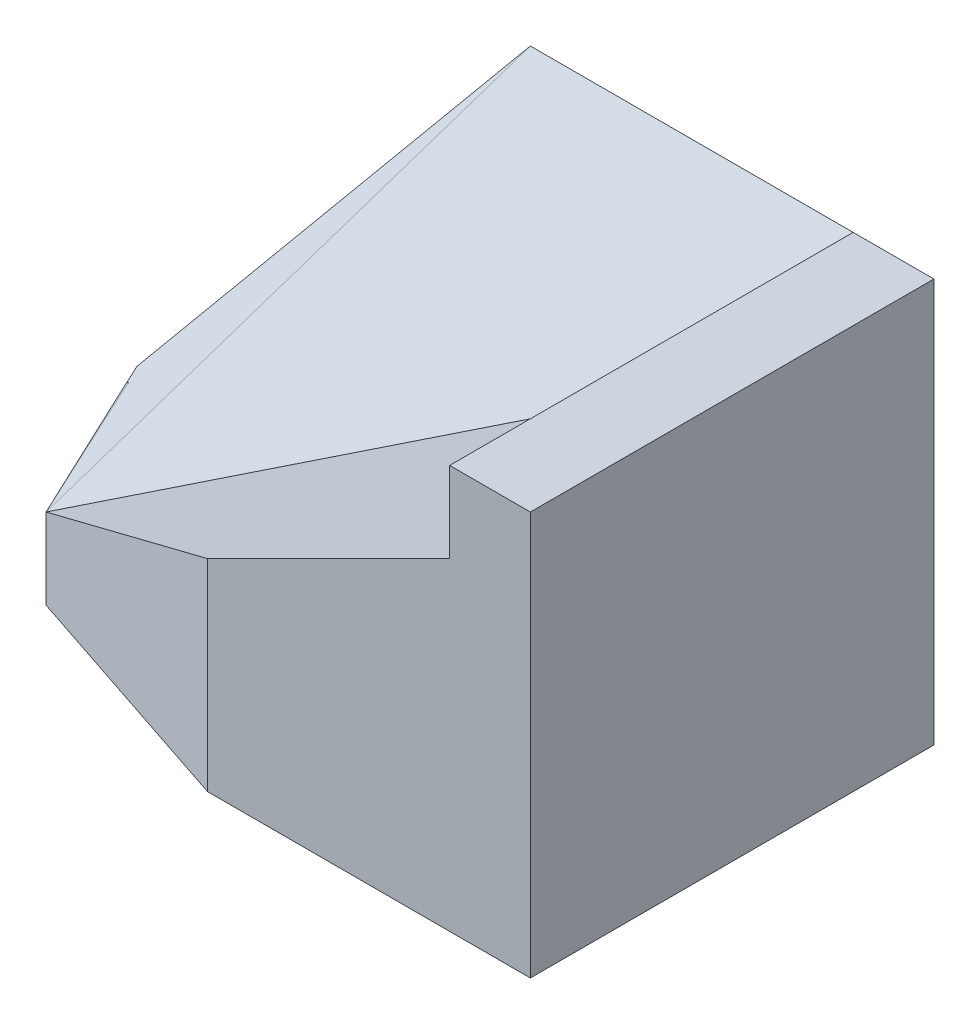
SolidWorks part; units mm, degrees
ref_plane "Front Plane" through (0, 0, 0) normal (0, 0, 1) x (1, 0, 0)
ref_plane "Top Plane" through (0, 0, 0) normal (0, 1, 0) x (1, 0, 0)
ref_plane "Right Plane" through (0, 0, 0) normal (1, 0, 0) x (0, 0, -1)
sketch "Sketch1" plane through (0, 0, 0) normal (0, 0, 1) x (1, 0, 0)
  line L1 (0, 0) -> (70, 0)
  line L2 (0, 0) -> (0, 50)
  line L3 (0, 50) -> (70, 50)
  line L4 (70, 0) -> (70, 50)
  dimension "D1" = 70
  dimension "D2" = 50
extrude "Boss-Extrude1" add sketch "Sketch1" along normal blind 50
sketch "Sketch2" plane through (0, 0, 50) normal (0, 0, 1) x (1, 0, 0)
  line L0 (0, 20) -> (20, 50)
  line L1 (0, 50) -> (0, 0) construction
  line L2 (70, 50) -> (0, 50) construction
  line L3 (20, 50) -> (0, 50)
  line L4 (0, 50) -> (0, 20)
  dimension "D1" = 20
  dimension "D2" = 30
extrude "Cut-Extrude1" cut sketch "Sketch2" against normal blind 50
sketch "Sketch3" plane through (0, 0, 0) normal (0, -1, 0) x (1, 0, 0)
  line L0 (0, 40) -> (30, 50)
  line L1 (0, 50) -> (0, 0) construction
  line L2 (0, 50) -> (70, 50) construction
  line L3 (30, 50) -> (0, 50)
  line L4 (0, 50) -> (0, 40)
  dimension "D1" = 10
  dimension "D2" = 30
extrude "Cut-Extrude2" cut sketch "Sketch3" against normal blind 50
sketch "Sketch4" plane through (0, 50, 0) normal (0, 1, 0) x (1, 0, 0)
  line L0 (70, 0) -> (20, 0) construction
  line L1 (60, 0) -> (20, 0)
  line L2 (60, 0) -> (60, -50)
  line L3 (60, -50) -> (20, -50)
  line L4 (20, 0) -> (20, -50)
  dimension "D1" = 10
  dimension "D2" = 40
  dimension "D3" = 50
extrude "Cut-Extrude4" cut sketch "Sketch4" against normal blind 30
ref_plane "Plane1" through (30, 0, 50) normal (0, -1, 0) x (-1, 0, 0)
sketch "Sketch6" plane through (0, 0, 50) normal (0, 0, 1) x (1, 0, 0)
  line L0 (30, 20) -> (30, 25)
  line L1 (30, 25) -> (60, 40)
  line L2 (60, 20) -> (60, 50) construction
  line L3 (60, 40) -> (60, 20)
  line L4 (60, 20) -> (30, 20)
  dimension "D1" = 5
  dimension "D2" = 15
extrude "Boss-Extrude2" add sketch "Sketch6" against normal blind 50
sketch "Sketch7" plane through (0, 0, 50) normal (0, 0, 1) x (1, 0, 0)
  line L0 (30, 25) -> (0, 10)
  line L1 (0, 10) -> (0, 0)
  line L2 (0, 0) -> (30, 0)
  line L3 (30, 0) -> (30, 25)
  dimension "D1" = 10
extrude "Boss-Extrude3" add sketch "Sketch7" against normal blind 50
sketch "Sketch8" plane through (0, 0, 0) normal (0, -1, 0) x (-1, 0, 0)
  line L0 (0, -40) -> (-30, -50)
  line L1 (0, -50) -> (0, 0) construction
  line L2 (0, -50) -> (-70, -50) construction
  line L3 (-30, -50) -> (0, -50)
  line L4 (0, -50) -> (0, -40)
  dimension "D1" = 10
  dimension "D2" = 30
extrude "Cut-Extrude5" cut sketch "Sketch8" against normal blind 50
sketch "Sketch10" plane through (0, 0, 50) normal (0, 0, 1) x (1, 0, 0)
  line L0 (30, 25) -> (0, 10)
  line L1 (0, 10) -> (0, 20)
  line L2 (0, 20) -> (30, 81.3244)
  line L3 (30, 81.3244) -> (30, 25)
  dimension "D1" = 10
  dimension "D2" = 10
  dimension "D3" = 0
  dimension "D4" = 68.2692
extrude "Cut-Extrude6" cut sketch "Sketch10" against normal blind 50 contours L3 L2 L1 L0
sketch "Sketch11" plane through (0, 50, 0) normal (0, 1, 0) x (1, 0, 0)
  line L0 (60, -50) -> (60, 0) construction
  point P0 (60, -10)
  dimension "D1" = 10
ref_plane "Plane2" through (-4.6154, 6.9231, 0) normal (0.5547, -0.8321, 0) x (-0.8321, -0.5547, 0)
sketch "Sketch12" plane through (-4.6154, 6.9231, 0) normal (0.5547, -0.8321, 0) x (-0.8321, -0.5547, 0)
  line L0 (-5.547, -40) -> (-77.658, -10)
  line L1 (-77.658, -10) -> (-5.547, 0)
  line L2 (-5.547, 0) -> (-5.547, -42.2593)
extrude "Boss-Extrude4" add sketch "Sketch12" along normal blind 50 contours L2 L1 L0
sketch "Sketch14" plane through (0, 0, 0) normal (0, 0, -1) x (-1, 0, 0)
  line L0 (-60, 50) -> (-20, 50)
  line L1 (-20, 50) -> (0, 20)
  line L2 (0, 20) -> (0, 10)
  line L3 (0, 10) -> (-60, 50)
  line L4 (-60, 50) -> (-60, 40)
  line L5 (-60, 40) -> (0, 10)
  line L6 (0, 10) -> (-0.0235, 10.1845)
  dimension "D1" = 30
  dimension "D2" = 20
extrude "Boss-Extrude7" add sketch "Sketch14" against normal blind 30
sketch "Sketch15" plane through (0, 0, 0) normal (0, -1, 0) x (1, 0, 0)
  line L1 (70, 0) -> (0, 0)
  line L2 (70, 0) -> (70, 40)
  line L3 (70, 40) -> (0, 40)
  line L4 (0, 0) -> (0, 40)
extrude "Cut-Extrude7" cut sketch "Sketch15" along normal blind 51
sketch "Sketch16" plane through (70, 0, 0) normal (1, 0, 0) x (0, 0, -1)
  line L1 (0, 50) -> (-48.1719, 50)
  line L2 (0, 50) -> (0, -15.238)
  line L3 (0, -15.238) -> (-48.1719, -15.238)
  line L4 (-48.1719, 50) -> (-48.1719, -15.238)
  dimension "D1" = 48.1719
  dimension "D2" = 65.238
extrude "Cut-Extrude8" cut sketch "Sketch16" along normal blind 51
sketch "Sketch17" plane through (-4, 8, 0) normal (-0.4472, 0.8944, 0) x (0.8944, 0.4472, 0)
  line L0 (4.4721, -40) -> (38.0132, -50)
  line L1 (38.0132, -50) -> (71.5542, -50)
  line L2 (71.5542, -50) -> (71.5542, -30)
  line L3 (71.5542, -30) -> (4.4721, -30)
  line L4 (4.4721, -30) -> (4.4721, -40)
extrude "Cut-Extrude9" cut sketch "Sketch17" along normal blind 51
ref_plane "Plane3" through (-5.5034, 24.7651, 22.0134) normal (-0.1638, 0.7373, 0.6554) x (0.9865, 0.1225, 0.1089)
sketch "Sketch18" plane through (-5.5034, 24.7651, 22.0134) normal (-0.1638, 0.7373, 0.6554) x (0.9865, 0.1225, 0.1089)
  line L0 (25.8527, 33.2182) -> (5.5787, -23.2527)
  line L1 (5.5787, -23.2527) -> (66.4007, 25.7441)
  line L2 (66.4007, 25.7441) -> (25.8527, 33.2182)
extrude "Cut-Extrude10" cut sketch "Sketch18" along normal blind 51
sketch "Sketch19" plane through (12.17, -1.4318, 4.6532) normal (0.9285, -0.1092, 0.355) x (0.3526, -0.0415, -0.9349)
  line L0 (-27.1127, 29.6172) -> (-27.1127, 20.4472)
  line L1 (-27.1127, 20.4472) -> (4.9774, 51.9944)
  line L2 (4.9774, 51.9944) -> (-27.1127, 29.6172)
extrude "Cut-Extrude11" cut sketch "Sketch19" against normal blind 51
sketch "Sketch20" plane through (-9.5591, 1.1246, 25.3468) normal (0.3526, -0.0415, -0.9349) x (-0.9358, -0.0156, -0.3522)
  line L0 (-10.6036, 19.2741) -> (-15.5582, 18.6506)
  line L1 (-15.5582, 18.6506) -> (-16.7031, 27.7488)
  line L2 (-16.7031, 27.7488) -> (-10.6036, 19.2741)
extrude "Cut-Extrude12" cut sketch "Sketch20" against normal blind 51
sketch "Sketch21" plane through (-5.5034, 24.7651, 22.0134) normal (-0.1638, 0.7373, 0.6554) x (0.9865, 0.1225, 0.1089)
  line L0 (25.8527, 33.2182) -> (66.4007, 25.7441)
  line L1 (66.4007, 25.7441) -> (5.5787, -23.2527)
  line L2 (5.5787, -23.2527) -> (5.9474, -7.4477)
  line L3 (5.9474, -7.4477) -> (25.8527, 33.2182)
extrude "Boss-Extrude8" add sketch "Sketch21" against normal blind 51
sketch "Sketch22" plane through (-5.5034, 24.7651, 22.0134) normal (-0.1638, 0.7373, 0.6554) x (0.9865, 0.1225, 0.1089)
  line L0 (25.8527, 33.2182) -> (5.9474, -7.4477)
  line L1 (5.9474, -7.4477) -> (5.5787, -23.2527)
  line L2 (5.5787, -23.2527) -> (66.4007, 25.7441)
  line L3 (66.4007, 25.7441) -> (25.8527, 33.2182)
extrude "Cut-Extrude13" cut sketch "Sketch22" along normal blind 51
sketch "Sketch23" plane through (6.0351, 0.6544, 0.7726) normal (0.9862, 0.1069, 0.1263) x (0.1255, 0.0136, -0.992)
  line L0 (-27.6761, 20.3865) -> (-29.4632, 20.1165)
  line L1 (-29.4632, 20.1165) -> (-29.4632, 18.8138)
  line L2 (-29.4632, 18.8138) -> (-27.6761, 20.3865)
extrude "Cut-Extrude14" cut sketch "Sketch23" against normal blind 51
sketch "Sketch24" plane through (-3.6981, -0.401, 29.2274) normal (0.1255, 0.0136, -0.992) x (-0.9921, 0.0017, -0.1255)
  line L0 (-3.7276, 20.4093) -> (-3.7276, 19.3333)
  line L1 (-3.7276, 19.3333) -> (-4.0389, 19.3673)
  line L2 (-4.0389, 19.3673) -> (-3.8973, 20.6623)
  line L3 (-3.8973, 20.6623) -> (-3.7276, 20.4093)
extrude "Cut-Extrude15" cut sketch "Sketch24" against normal blind 51
sketch "Sketch25" plane through (0, 0, 0) normal (-1, 0, 0) x (0, 0, 1)
  line L0 (30, 10) -> (40, 10)
  line L1 (40, 10) -> (30, 18.924)
  line L2 (30, 18.924) -> (30, 10)
extrude "Boss-Extrude9" add sketch "Sketch25" against normal blind 51
sketch "Sketch26" plane through (-5.5034, 24.7651, 22.0134) normal (-0.1638, 0.7373, 0.6554) x (0.9865, 0.1225, 0.1089)
  line L0 (5.5787, -8.2007) -> (5.5787, -23.2527)
  line L1 (5.5787, -23.2527) -> (25.8527, 33.2182)
  line L2 (25.8527, 33.2182) -> (5.5787, -8.2007)
extrude "Boss-Extrude10" add sketch "Sketch26" against normal blind 51
sketch "Sketch27" plane through (-5.5034, 24.7651, 22.0134) normal (-0.1638, 0.7373, 0.6554) x (0.9865, 0.1225, 0.1089)
  line L0 (5.5787, -23.2527) -> (5.5787, -8.2007)
  line L1 (5.5787, -8.2007) -> (12.707, -17.5104)
  line L2 (5.5787, -23.2527) -> (25.8527, -6.9205) construction
  line L3 (12.707, -17.5104) -> (5.5787, -23.2527)
  dimension "D1" = 9.1535
extrude "Boss-Extrude11" add sketch "Sketch27" against normal blind 51
sketch "Sketch28" plane through (0, 0, 0) normal (0, 0, -1) x (-1, 0, 0)
  line L1 (-70, 50) -> (0, 50)
  line L2 (-70, 50) -> (-70, 0)
  line L3 (-70, 0) -> (0, 0)
  line L4 (0, 50) -> (0, 0)
extrude "Cut-Extrude16" cut sketch "Sketch28" along normal blind 51
sketch "Sketch29" plane through (0, 0, 0) normal (0, -1, 0) x (1, 0, 0)
  line L1 (70, 50) -> (0, 50)
  line L2 (70, 50) -> (70, -34.422)
  line L3 (70, -34.422) -> (0, -34.422)
  line L4 (0, 50) -> (0, -34.422)
  dimension "D1" = 70
  dimension "D2" = 84.422
extrude "Cut-Extrude17" cut sketch "Sketch29" along normal blind 51
sketch "Sketch30" plane through (-4, 8, 0) normal (-0.4472, 0.8944, 0) x (0.8944, 0.4472, 0)
  line L0 (4.4721, -40) -> (71.5542, -50)
  line L1 (71.5542, -50) -> (71.5542, -10)
  line L2 (71.5542, -10) -> (4.4721, -40)
  dimension "D1" = 40
extrude "Cut-Extrude18" cut sketch "Sketch30" along normal blind 51
sketch "Sketch31" plane through (0, 0, 30) normal (0, 0, 1) x (1, 0, 0)
  line L0 (55, 50) -> (60, 50)
  line L1 (60, 50) -> (55, 50) construction
  line L2 (60, 50) -> (60, 40)
  line L3 (60, 40) -> (55, 50)
extrude "Cut-Extrude19" cut sketch "Sketch31" against normal blind 20
sketch "Sketch32" plane through (-5.5034, 24.7651, 22.0134) normal (-0.1638, 0.7373, 0.6554) x (0.9865, 0.1225, 0.1089)
  line L0 (66.4007, 25.7441) -> (5.5787, -23.2527)
  line L1 (5.5787, -23.2527) -> (5.5787, -8.2007)
  line L2 (5.5787, -8.2007) -> (25.8527, 33.2182)
  line L3 (25.8527, 33.2182) -> (66.4007, 25.7441)
extrude "Boss-Extrude12" add sketch "Sketch32" against normal blind 20
ref_plane "Plane4" through (0, 25, 25) normal (0, -0.7071, -0.7071) x (-1, 0, 0)
sketch "Sketch33" plane through (0, 25, 25) normal (0, -0.7071, -0.7071) x (-1, 0, 0)
  line L0 (-20, 35.3553) -> (-60, 21.2132)
  line L1 (-60, 21.2132) -> (0, -21.2132)
  line L2 (0, -21.2132) -> (-20, 35.3553)
ref_plane "Plane7" through (0, 25, 25) normal (0, -0.7071, -0.7071) x (-1, 0, 0)
sketch "Sketch40" plane through (0, 25, 25) normal (0, -0.7071, -0.7071) x (-1, 0, 0)
  line L0 (-60, 21.2132) -> (0, -21.2132)
  line L1 (0, -21.2132) -> (-20, 35.3553)
  line L2 (-20, 35.3553) -> (-60, 21.2132)
extrude "Cut-Extrude24" cut sketch "Sketch40" against normal blind 20
sketch "Sketch41" plane through (0, 25, 25) normal (0, 0.7071, 0.7071) x (1, 0, 0)
  line L0 (20, -7.0711) -> (17.6271, -7.0711)
  line L1 (17.6271, -7.0711) -> (0, -21.2132)
  line L2 (0, -21.2132) -> (20, -7.0711)
extrude "Boss-Extrude14" add sketch "Sketch41" against normal blind 20
sketch "Sketch42" plane through (0, 25, 25) normal (0, -0.7071, -0.7071) x (-1, 0, 0)
  line L0 (-60, 21.2132) -> (-70, 35.3553)
  line L1 (-70, 35.3553) -> (-20, 35.3553)
  line L2 (-20, 35.3553) -> (-60, 21.2132)
extrude "Cut-Extrude25" cut sketch "Sketch42" against normal blind 20
sketch "Sketch43" plane through (0, 50, 0) normal (0, 1, 0) x (1, 0, 0)
  line L1 (60, -20) -> (70, -20)
  line L2 (60, -20) -> (60, 0)
  line L3 (60, 0) -> (70, 0)
  line L4 (70, -20) -> (70, 0)
extrude "Boss-Extrude15" add sketch "Sketch43" against normal blind 20
sketch "Sketch44" plane through (0, 0, 0) normal (0, 0, -1) x (-1, 0, 0)
  line L1 (0, 0) -> (-70, 0)
  line L2 (0, 0) -> (0, 50)
  line L3 (0, 50) -> (-70, 50)
  line L4 (-70, 0) -> (-70, 50)
extrude "Cut-Extrude26" cut sketch "Sketch44" along normal blind 20
sketch "Sketch45" plane through (0, 0, 0) normal (0, -1, 0) x (1, 0, 0)
  line L1 (0, 0) -> (70, 0)
  line L2 (0, 0) -> (0, 50)
  line L3 (0, 50) -> (70, 50)
  line L4 (70, 0) -> (70, 50)
extrude "Cut-Extrude27" cut sketch "Sketch45" along normal blind 20
